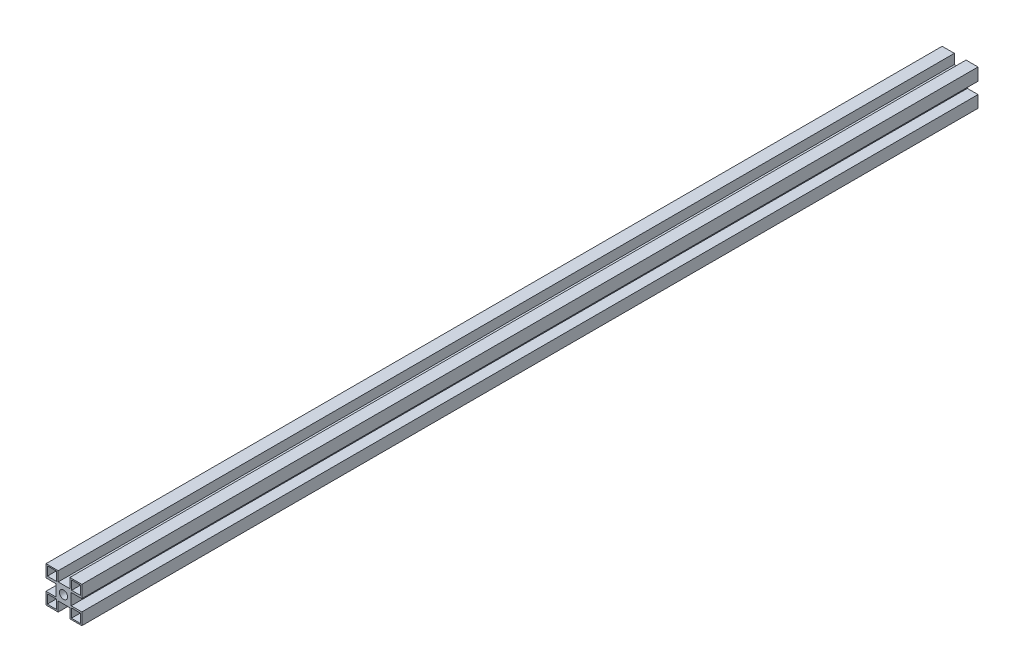
SolidWorks part; units mm, degrees
ref_plane "Alzado" through (0, 0, 0) normal (0, 0, 1) x (1, 0, 0)
ref_plane "Planta" through (0, 0, 0) normal (0, 1, 0) x (1, 0, 0)
ref_plane "Vista lateral" through (0, 0, 0) normal (1, 0, 0) x (0, 0, -1)
sketch "Croquis1" plane through (0, 0, 0) normal (0, 0, 1) x (1, 0, 0)
  line L0 (-19.6413, 22.4089) -> (-14.6413, 22.4089)
  line L1 (-33.9486, 23.1395) -> (-27.1367, 23.1395)
  line L2 (-33.9486, 23.1395) -> (-33.9486, 16.2369)
  line L3 (-33.9486, 3.1395) -> (-27.1367, 3.1395)
  line L4 (-13.9486, 23.1395) -> (-13.9486, 16.2369)
  line L5 (-33.1873, 22.4895) -> (-28.1873, 22.4895)
  line L6 (-33.1873, 22.4895) -> (-33.1873, 17.4895)
  line L7 (-33.1873, 17.4895) -> (-28.1873, 17.4895)
  line L8 (-28.1873, 22.4895) -> (-28.1873, 17.4895)
  line L9 (-19.6413, 22.4089) -> (-19.6413, 17.4089)
  line L10 (-19.6413, 17.4089) -> (-14.6413, 17.4089)
  line L11 (-14.6413, 22.4089) -> (-14.6413, 17.4089)
  line L12 (-19.7804, 8.8587) -> (-14.7804, 8.8587)
  line L13 (-19.7804, 8.8587) -> (-19.7804, 3.8587)
  line L14 (-19.7804, 3.8587) -> (-14.7804, 3.8587)
  line L15 (-14.7804, 8.8587) -> (-14.7804, 3.8587)
  line L16 (-33.225, 8.9517) -> (-28.225, 8.9517)
  line L17 (-33.225, 8.9517) -> (-33.225, 3.9517)
  line L18 (-33.225, 3.9517) -> (-28.225, 3.9517)
  line L19 (-28.225, 8.9517) -> (-28.225, 3.9517)
  line L20 (-20.631, 23.1395) -> (-13.9486, 23.1395)
  line L21 (-13.9486, 9.8089) -> (-13.9486, 3.1395)
  line L22 (-27.1367, 3.1395) -> (-27.1367, 8.5129)
  line L23 (-27.1367, 8.5129) -> (-20.631, 8.5129)
  line L24 (-20.631, 3.1395) -> (-20.631, 8.5129)
  line L25 (-33.9486, 9.8089) -> (-33.9486, 3.1395)
  line L26 (-27.1367, 23.1395) -> (-27.1367, 17.7168)
  line L27 (-27.1367, 17.7168) -> (-20.631, 17.7168)
  line L28 (-20.631, 23.1395) -> (-20.631, 17.7168)
  line L29 (-13.9486, 16.2369) -> (-19.8793, 16.2369)
  line L31 (-13.9486, 9.8089) -> (-19.8793, 9.8089)
  line L32 (-19.8793, 16.2369) -> (-19.8793, 9.8089)
  line L33 (-33.9486, 9.8089) -> (-28.4351, 9.8089)
  line L34 (-20.631, 3.1395) -> (-13.9486, 3.1395)
  line L35 (-33.9486, 16.2369) -> (-28.4351, 16.2369)
  line L36 (-28.4351, 9.8089) -> (-28.4351, 16.2369)
  circle A0 centre (-24.1906, 13.0719) radius 2.2702
  dimension "D1" = 20
  dimension "D2" = 5
  dimension "D3" = 5
extrude "Saliente-Extruir1" add sketch "Croquis1" along normal blind 500
